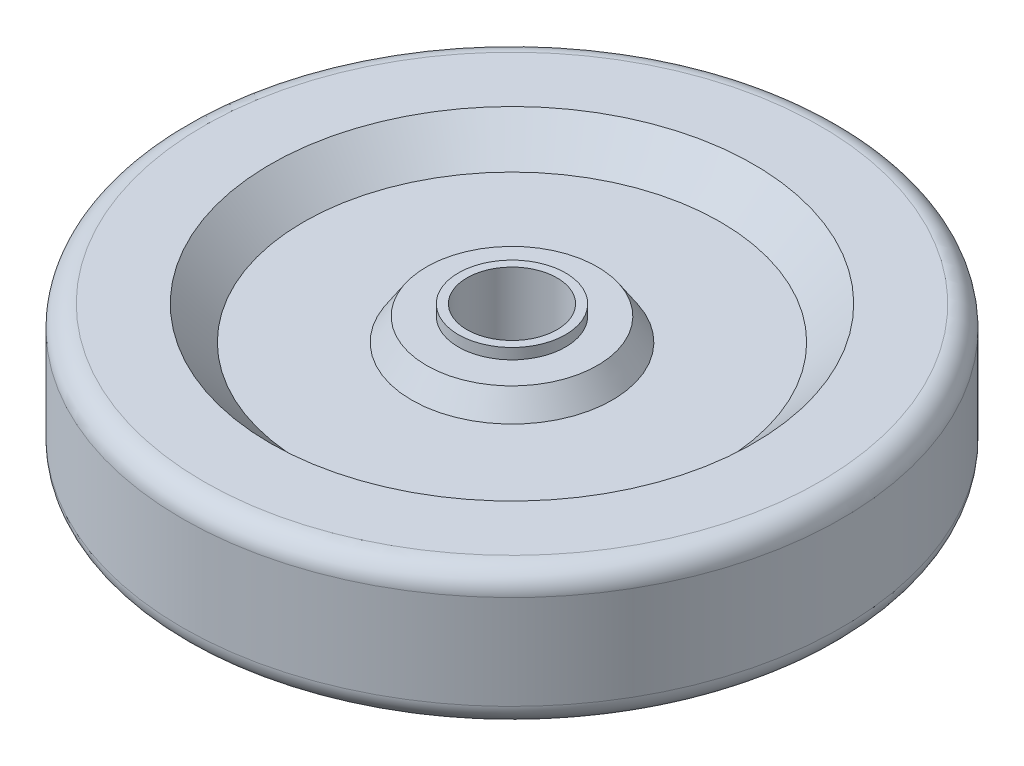
SolidWorks part; units mm, degrees
ref_plane "Спереди" through (0, 0, 0) normal (0, 0, 1) x (1, 0, 0)
ref_plane "Сверху" through (0, 0, 0) normal (0, 1, 0) x (1, 0, 0)
ref_plane "Справа" through (0, 0, 0) normal (1, 0, 0) x (0, 0, -1)
sketch "Эскиз2" plane through (0, 0, 0) normal (1, 0, 0) x (0, 0, -1)
  line L0 (0, 76.5842) -> (0, -47.4093) construction
  line L1 (10.5, 0) -> (10.5, 32)
  line L2 (10.5, 32) -> (12.5, 32)
  line L3 (12.5, 32) -> (12.5, 29.5)
  line L4 (12.5, 29.5) -> (19.9443, 29.5)
  line L5 (19.9443, 29.5) -> (23.4129, 24.2369)
  line L6 (23.4129, 24.2369) -> (48.6268, 24.2369)
  line L7 (12.5, 2.5) -> (19.9443, 2.5)
  line L8 (19.9443, 2.5) -> (23.4129, 5.9686)
  line L9 (23.4129, 5.9686) -> (48.6438, 5.9686)
  line L10 (48.6268, 24.2369) -> (56.39, 32)
  line L11 (12.5, 2.5) -> (12.5, 0)
  line L12 (12.5, 0) -> (10.5, 0)
  line L13 (56.39, 32) -> (71.9091, 32)
  line L14 (76.9091, 27) -> (76.9091, 5)
  line L15 (71.9091, 0) -> (56.39, 0)
  line L16 (56.39, 0) -> (48.6438, 5.9686)
  arc A0 (76.9091, 5) -> (71.9091, 0) centre (71.9091, 5) cw
  arc A1 (71.9091, 32) -> (76.9091, 27) centre (71.9091, 27) cw
  dimension "D1" = 5
revolve "Повернуть1" add sketch "Эскиз2" angle 360 about L0
